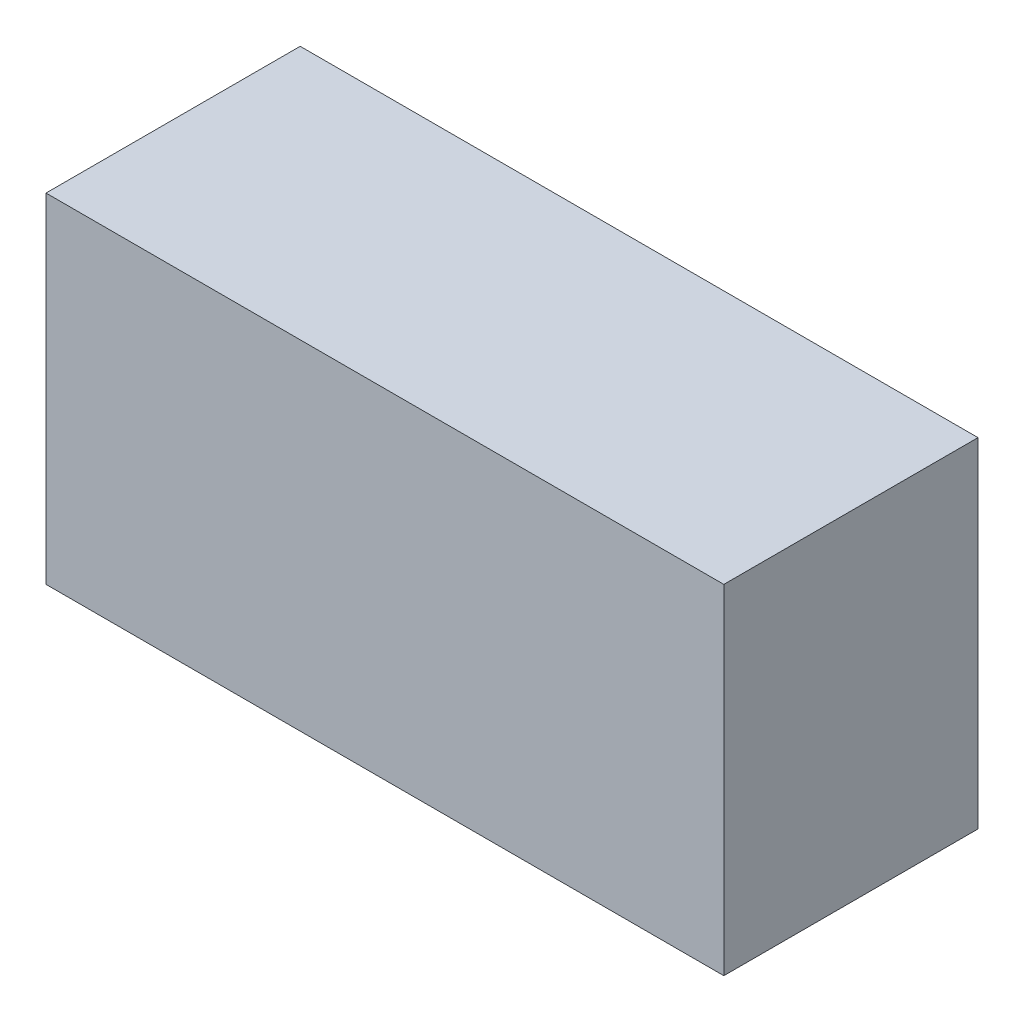
SolidWorks part; units mm, degrees
ref_plane "Front Plane" through (0, 0, 0) normal (0, 0, 1) x (1, 0, 0)
ref_plane "Top Plane" through (0, 0, 0) normal (0, 1, 0) x (1, 0, 0)
ref_plane "Right Plane" through (0, 0, 0) normal (1, 0, 0) x (0, 0, -1)
sketch "Sketch2" plane through (0, 0, 0) normal (0, 0, 1) x (1, 0, 0)
  line L1 (-20, -10) -> (20, -10)
  line L2 (-20, -10) -> (-20, 10)
  line L3 (-20, 10) -> (20, 10)
  line L4 (20, -10) -> (20, 10)
  line L5 (-20, -10) -> (20, 10) construction
  line L6 (-20, 10) -> (20, -10) construction
  point P0 (0, 0)
  dimension "D1" = 40
  dimension "D2" = 20
extrude "Boss-Extrude1" add sketch "Sketch2" along normal blind 15
